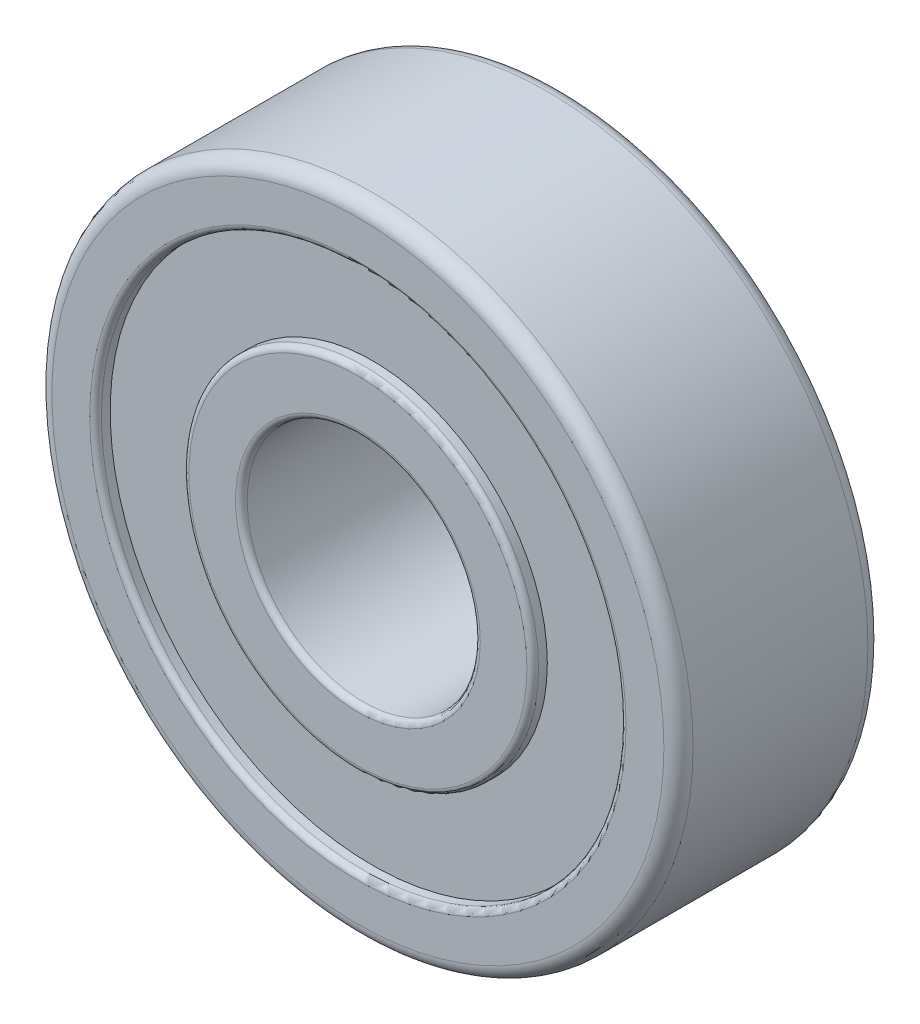
SolidWorks part; units mm, degrees
ref_plane "Ön Düzlem" through (0, 0, 0) normal (0, 0, 1) x (1, 0, 0)
ref_plane "Üst Düzlem" through (0, 0, 0) normal (0, 1, 0) x (1, 0, 0)
ref_plane "Sağ Düzlem" through (0, 0, 0) normal (1, 0, 0) x (0, 0, -1)
sketch "Çizim1" plane through (0, 0, 0) normal (0, 0, 1) x (1, 0, 0)
  circle A0 centre (0, 0) radius 4
  circle A1 centre (0, 0) radius 11
  dimension "D1" = 8
  dimension "D2" = 22
extrude "Yükseklik-Ekstrüzyon1" add sketch "Çizim1" along normal blind 7
sketch "Çizim2" plane through (0, 0, 0) normal (0, 0, -1) x (-1, 0, 0)
  circle A0 centre (0, 0) radius 6
  circle A1 centre (0, 0) radius 9
  dimension "D1" = 12
  dimension "D2" = 18
extrude "Kes-Ekstrüzyon1" cut sketch "Çizim2" against normal blind 0.5
sketch "Çizim3" plane through (0, 0, 7) normal (0, 0, 1) x (1, 0, 0)
  circle A0 centre (0, 0) radius 6
  circle A1 centre (0, 0) radius 9
  dimension "D1" = 12
  dimension "D2" = 18
extrude "Kes-Ekstrüzyon2" cut sketch "Çizim3" against normal blind 0.5
fillet "Radyus1" radius 0.5 2 edges at (11, 0, 7) (11, 0, 0)
fillet "Radyus2" radius 0.2 6 edges at (4, 0, 7) (4, 0, 0) (6, 0, 7) (9, 0, 7) (-6, 0, 0) (-9, 0, 0)
